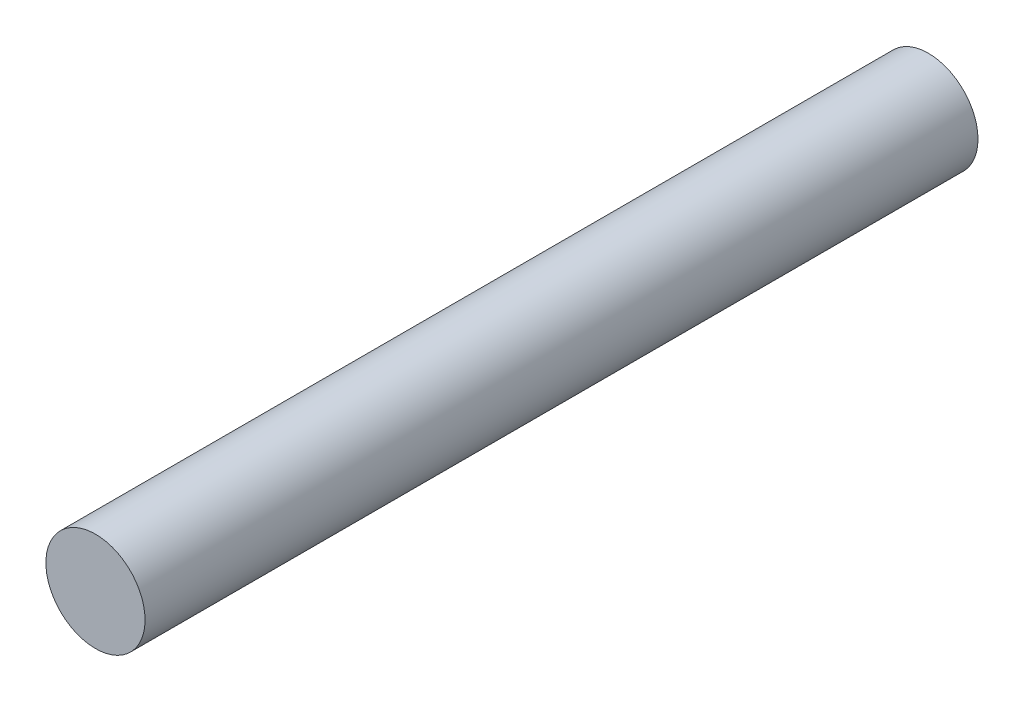
SolidWorks part; units mm, degrees
ref_plane "Plan de face" through (0, 0, 0) normal (0, 0, 1) x (1, 0, 0)
ref_plane "Plan de dessus" through (0, 0, 0) normal (0, 1, 0) x (1, 0, 0)
ref_plane "Plan de droite" through (0, 0, 0) normal (1, 0, 0) x (0, 0, -1)
sketch "Esquisse1" plane through (0, 0, 0) normal (0, 0, 1) x (1, 0, 0)
  circle A0 centre (-8.7667, 13.0588) radius 2.5
extrude "Boss.-Extru.3" add sketch "Esquisse1" along normal blind 42 contours A0
